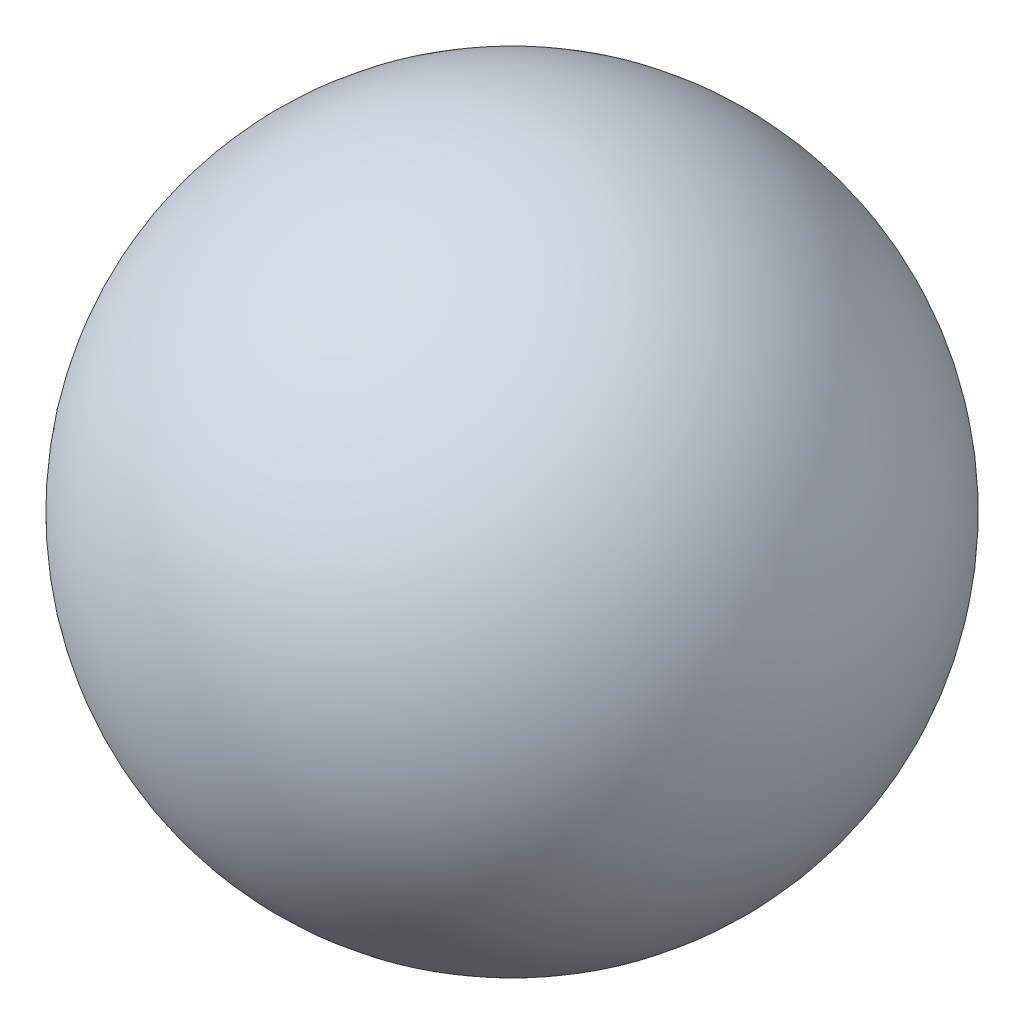
SolidWorks part; units mm, degrees
ref_plane "Front Plane" through (0, 0, 0) normal (0, 0, 1) x (1, 0, 0)
ref_plane "Top Plane" through (0, 0, 0) normal (0, 1, 0) x (1, 0, 0)
ref_plane "Right Plane" through (0, 0, 0) normal (1, 0, 0) x (0, 0, -1)
sketch "Sketch1" plane through (0, 0, 0) normal (0, 0, 1) x (1, 0, 0)
  line L0 (0, 254) -> (0, 0)
  arc A0 (0, 254) -> (0, 0) centre (0, 127) cw
  dimension "D1" = 254
revolve "Revolve1" add sketch "Sketch1" angle 360 about L0
